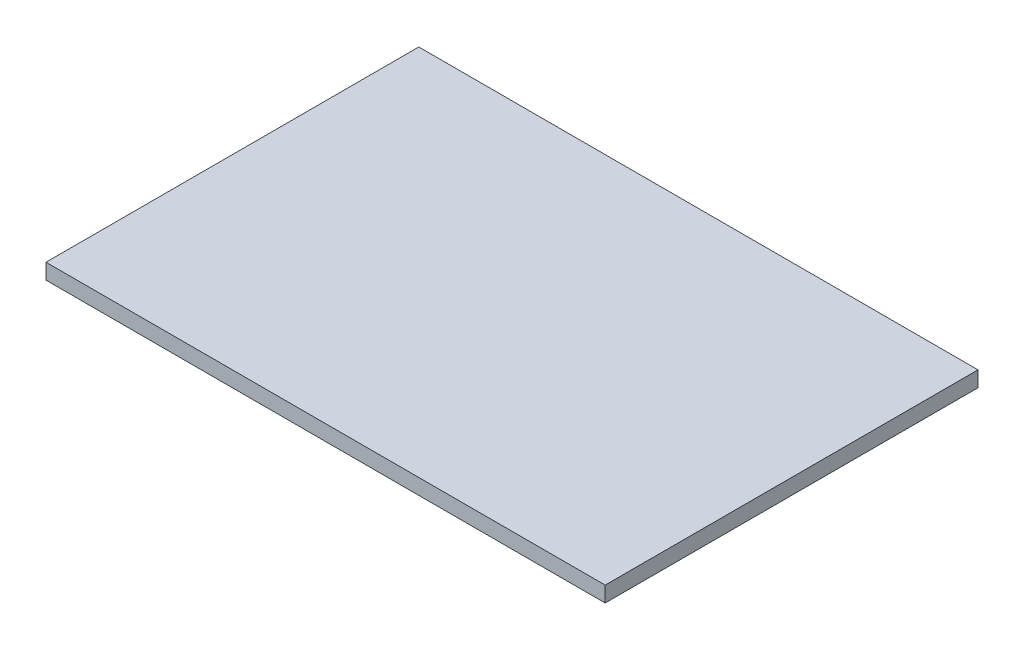
SolidWorks part; units mm, degrees
ref_plane "前视基准面" through (0, 0, 0) normal (0, 0, 1) x (1, 0, 0)
ref_plane "上视基准面" through (0, 0, 0) normal (0, 1, 0) x (1, 0, 0)
ref_plane "右视基准面" through (0, 0, 0) normal (1, 0, 0) x (0, 0, -1)
sketch "草图1" plane through (0, 0, 0) normal (0, 1, 0) x (1, 0, 0)
  line L1 (-90, -60) -> (90, -60)
  line L2 (-90, -60) -> (-90, 60)
  line L3 (-90, 60) -> (90, 60)
  line L4 (90, -60) -> (90, 60)
  line L5 (-90, -60) -> (90, 60) construction
  line L6 (-90, 60) -> (90, -60) construction
  point P0 (0, 0)
  dimension "D1" = 180
  dimension "D2" = 120
extrude "凸台-拉伸1" add sketch "草图1" along normal blind 5
